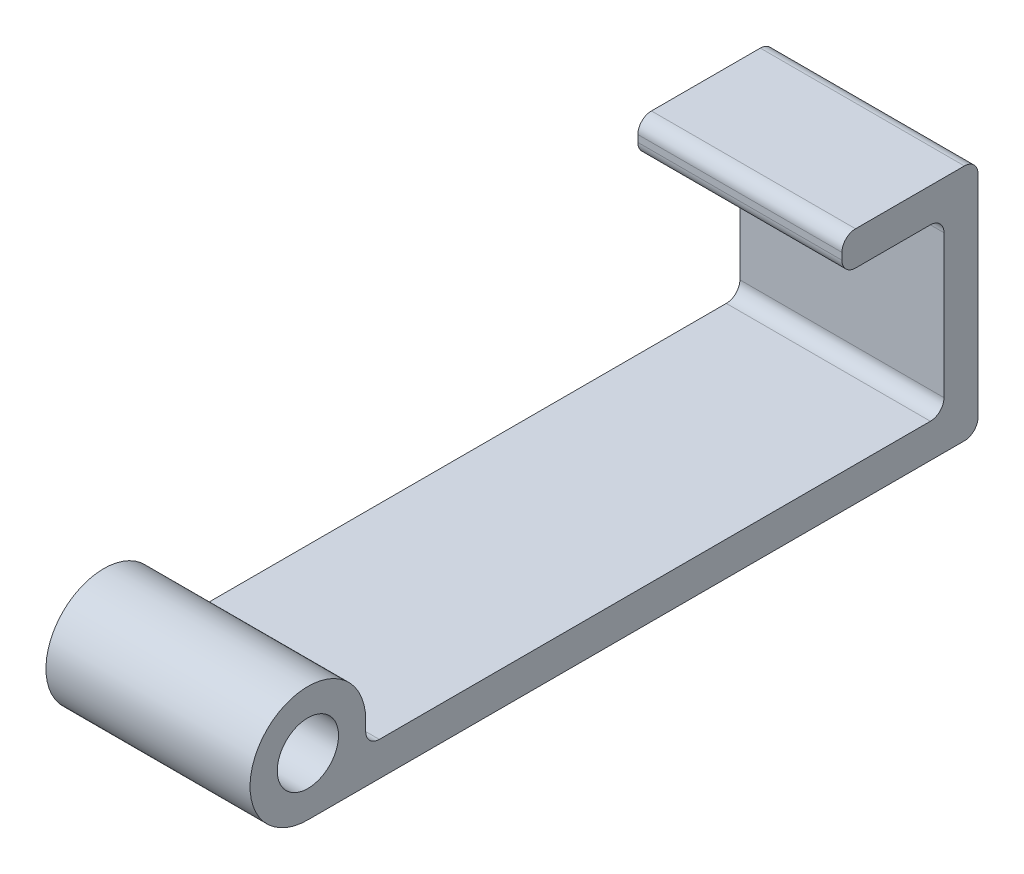
SolidWorks part; units mm, degrees
ref_plane "Front Plane" through (0, 0, 0) normal (0, 0, 1) x (1, 0, 0)
ref_plane "Top Plane" through (0, 0, 0) normal (0, 1, 0) x (1, 0, 0)
ref_plane "Right Plane" through (0, 0, 0) normal (1, 0, 0) x (0, 0, -1)
sketch "Sketch1" plane through (0, 0, 0) normal (0, 1, 0) x (1, 0, 0)
  line L1 (-15, 42.5) -> (15, 42.5)
  line L2 (-15, 42.5) -> (-15, -42.5)
  line L3 (-15, -42.5) -> (15, -42.5)
  line L4 (15, 42.5) -> (15, -42.5)
  point P4 (-15, 0)
  point P6 (0, 42.5)
  dimension "D1" = 85
  dimension "D2" = 30
extrude "Boss-Extrude1" add sketch "Sketch1" along normal blind 5
sketch "Sketch2" plane through (15, 0, 0) normal (1, 0, 0) x (0, 0, -1)
  line L0 (-42.5, 0) -> (42.5, 0) construction
  line L1 (42.5, 0) -> (47.5, 0)
  line L2 (42.5, 0) -> (42.5, 30)
  line L3 (42.5, 30) -> (47.5, 30)
  line L4 (47.5, 0) -> (47.5, 30)
  line L5 (47.5, 30) -> (27.5, 30)
  line L6 (47.5, 30) -> (47.5, 35)
  line L7 (47.5, 35) -> (27.5, 35)
  line L8 (27.5, 30) -> (27.5, 35)
  line L9 (-42.5, 5) -> (-42.5, 0) construction
  line L10 (-42.5, 5) -> (-42.5, 8.5)
  line L11 (-42.5, 0) -> (-51, 0)
  line L12 (-42.5, 5) -> (-42.5, 0)
  circle A0 centre (-51, 8.5) radius 4.5
  arc A1 (-42.5, 8.5) -> (-51, 0) centre (-51, 8.5) ccw
  line M15 (42.5, 0) -> (42.5, 5)
  line M17 (-42.5, 5) -> (-42.5, 0)
  dimension "D5" = 9
  dimension "D6" = 17
  dimension "D1" = 30
  dimension "D2" = 5
  dimension "D3" = 20
  dimension "D4" = 5
extrude "Boss-Extrude2" add sketch "Sketch2" against normal blind 30 contours L10 A1 L11 A0 M17 | L1 L4 L3 L2 M15 | L8 L5 L3 L6 L7
fillet "Fillet1" radius 2 7 edges at (0, 5, 42.5) (0, 30, -42.5) (0, 5, -42.5) (0, 30, -27.5) (0, 0, -47.5) (0, 35, -47.5) (0, 35, -27.5)
